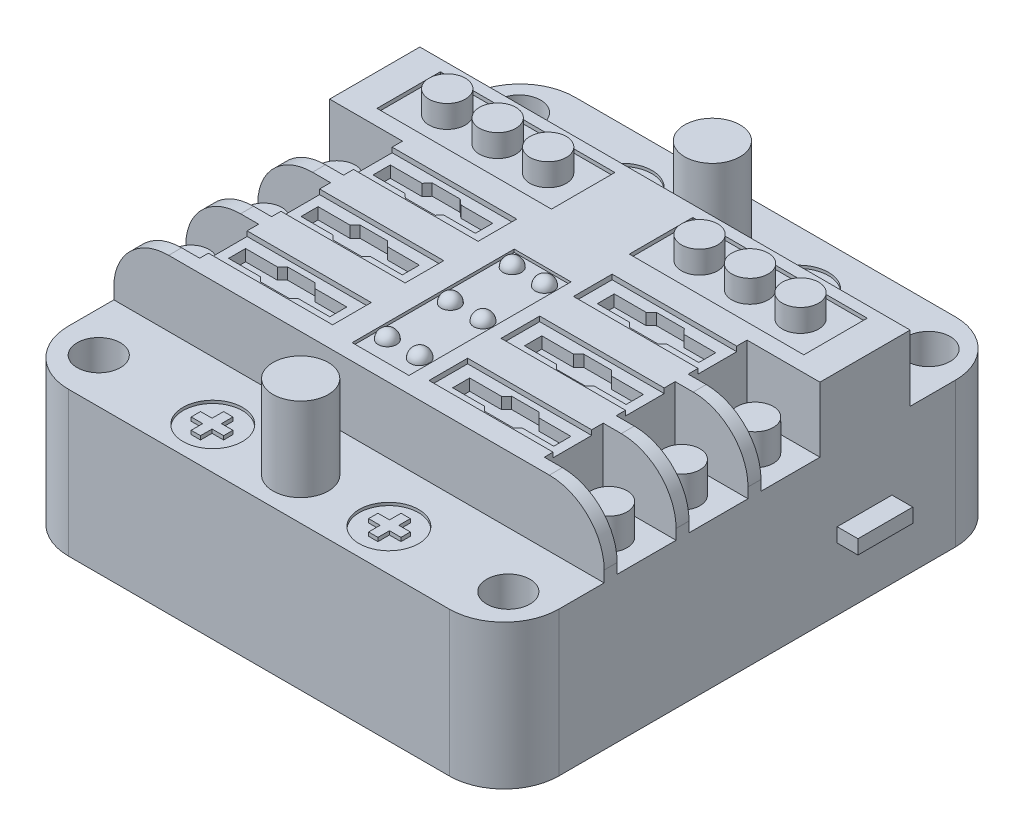
SolidWorks part; units mm, degrees
ref_plane "Front Plane" through (0, 0, 0) normal (0, 0, 1) x (1, 0, 0)
ref_plane "Top Plane" through (0, 0, 0) normal (0, 1, 0) x (1, 0, 0)
ref_plane "Right Plane" through (0, 0, 0) normal (1, 0, 0) x (0, 0, -1)
sketch "Sketch1" plane through (0, 0, 0) normal (0, 1, 0) x (1, 0, 0)
  line L1 (42.5, -43.875) -> (-42.5, -43.875)
  line L2 (42.5, -43.875) -> (42.5, 43.875)
  line L3 (42.5, 43.875) -> (-42.5, 43.875)
  line L4 (-42.5, -43.875) -> (-42.5, 43.875)
  line L5 (42.5, -43.875) -> (-42.5, 43.875) construction
  line L6 (42.5, 43.875) -> (-42.5, -43.875) construction
  point P0 (0, 0)
  dimension "D1" = 87.75
  dimension "D2" = 85
extrude "Boss-Extrude1" add sketch "Sketch1" along normal blind 36.5
sketch "Sketch2" plane through (0, 36.5, 0) normal (0, 1, 0) x (1, 0, 0)
  line L0 (-42.5, 43.875) -> (-42.5, 26.525)
  line L1 (-42.5, 43.875) -> (-42.5, -43.875) construction
  line L2 (-42.5, 26.525) -> (42.5, 26.525)
  line L3 (42.5, -43.875) -> (42.5, 43.875) construction
  line L4 (42.5, 26.525) -> (42.5, 43.875)
  line L5 (42.5, 43.875) -> (-42.5, 43.875)
  dimension "D1" = 17.35
extrude "Cut-Extrude1" cut sketch "Sketch2" against normal blind 11.44
sketch "Sketch3" plane through (0, 36.5, 0) normal (0, 1, 0) x (1, 0, 0)
  line L0 (-42.5, -26.525) -> (-42.5, -43.875)
  line L1 (-42.5, 26.525) -> (-42.5, -43.875) construction
  line L2 (-42.5, -43.875) -> (42.5, -43.875)
  line L3 (42.5, -43.875) -> (42.5, -26.525)
  line L4 (42.5, -43.875) -> (42.5, 26.525) construction
  line L5 (42.5, -26.525) -> (-42.5, -26.525)
  dimension "D1" = 17.35
extrude "Cut-Extrude2" cut sketch "Sketch3" against normal blind 11.44
sketch "Sketch5" plane through (0, 25.06, 0) normal (0, 1, 0) x (1, 0, 0)
  circle A0 centre (0, -36.634) radius 4.8
  dimension "D1" = 9.6
extrude "Boss-Extrude2" add sketch "Sketch5" along normal blind 14.5
sketch "Sketch6" plane through (0, 25.06, 0) normal (0, 1, 0) x (1, 0, 0)
  circle A0 centre (0, 34.7363) radius 4.8
  dimension "D1" = 9.6
extrude "Boss-Extrude3" add sketch "Sketch6" along normal blind 14.5
sketch "Sketch7" plane through (0, 25.06, 0) normal (0, 1, 0) x (1, 0, 0)
  line L0 (-42.5, 43.875) -> (-42.5, 26.525) construction
  line L1 (42.5, 26.525) -> (42.5, 43.875) construction
  circle A0 centre (-35.5, 36.7165) radius 3.75
  circle A1 centre (35.5, 36.7165) radius 3.75
  dimension "D2" = 7.5
  dimension "D3" = 7.5
  dimension "D1" = 7
  dimension "D4" = 7
extrude "Cut-Extrude3" cut sketch "Sketch7" against normal blind 26.5
sketch "Sketch8" plane through (0, 25.06, 0) normal (0, 1, 0) x (1, 0, 0)
  line L0 (-42.5, -26.525) -> (-42.5, -43.875) construction
  line L1 (42.5, -43.875) -> (42.5, -26.525) construction
  circle A0 centre (-35.5, -36.139) radius 3.75
  circle A1 centre (35.5, -36.139) radius 3.75
  point P6 (0, 0)
  dimension "D1" = 7.5
  dimension "D4" = 7.5
  dimension "D2" = 7
  dimension "D3" = 7
extrude "Cut-Extrude4" cut sketch "Sketch8" against normal blind 26.5
sketch "Sketch9" plane through (0, 36.5, 0) normal (0, 1, 0) x (1, 0, 0)
  line L0 (29.87, -14.055) -> (42.5, -14.055)
  line L1 (42.5, -26.525) -> (42.5, 26.525) construction
  line L2 (42.5, -24.275) -> (29.87, -24.275)
  line L3 (29.87, -24.275) -> (29.87, -14.055)
  line L4 (42.5, -14.055) -> (42.5, -24.275)
  line L5 (42.5, -11.805) -> (29.87, -11.805)
  line L6 (29.87, -11.805) -> (29.87, -1.585)
  line L7 (29.87, -1.585) -> (42.5, -1.585)
  line L8 (42.5, 0.665) -> (29.87, 0.665)
  line L9 (29.87, 0.665) -> (29.87, 10.885)
  line L10 (29.87, 10.885) -> (42.5, 10.885)
  line L11 (42.5, 10.885) -> (42.5, 0.665)
  line L12 (42.5, -1.585) -> (42.5, -11.805)
  line L13 (42.5, -26.525) -> (-42.5, -26.525) construction
  dimension "D1" = 10.22
  dimension "D2" = 10.22
  dimension "D3" = 2.25
  dimension "D4" = 10.22
  dimension "D5" = 2.25
  dimension "D6" = 12.63
  dimension "D7" = 2.25
extrude "Cut-Extrude5" cut sketch "Sketch9" against normal blind 11.27
fillet "Fillet1" radius 9.5 3 edges at (42.5, 36.5, 25.4) (42.5, 36.5, 12.93) (42.5, 36.5, 0.46)
sketch "Sketch10" plane through (0, 36.5, 0) normal (0, 1, 0) x (1, 0, 0)
  line L0 (-42.5, -24.275) -> (-29.87, -24.275)
  line L1 (-42.5, 26.525) -> (-42.5, -26.525) construction
  line L2 (-29.87, -24.275) -> (-29.87, -14.055)
  line L3 (-29.87, -14.055) -> (-42.5, -14.055)
  line L4 (-42.5, -14.055) -> (-42.5, -24.275)
  line L5 (-42.5, -11.805) -> (-29.87, -11.805)
  line L6 (-29.87, -11.805) -> (-29.87, -1.585)
  line L7 (-29.87, -1.585) -> (-42.5, -1.585)
  line L8 (-42.5, -1.585) -> (-42.5, -11.805)
  line L9 (-42.5, 0.665) -> (-29.87, 0.665)
  line L10 (-29.87, 0.665) -> (-29.87, 10.885)
  line L11 (-29.87, 10.885) -> (-42.5, 10.885)
  line L12 (-42.5, 10.885) -> (-42.5, 0.665)
  line L13 (42.5, -26.525) -> (-42.5, -26.525) construction
  dimension "D1" = 2.25
  dimension "D2" = 12.63
  dimension "D3" = 10.22
  dimension "D4" = 12.63
  dimension "D5" = 10.22
  dimension "D6" = 12.63
  dimension "D7" = 10.22
  dimension "D8" = 2.25
  dimension "D9" = 2.25
extrude "Cut-Extrude6" cut sketch "Sketch10" against normal blind 11.27
fillet "Fillet2" radius 9.5 3 edges at (-42.5, 36.5, 25.4) (-42.5, 36.5, 12.93) (-42.5, 36.5, 0.46)
sketch "Sketch12" plane through (0, 25.23, 0) normal (0, 1, 0) x (1, 0, 0)
  circle A0 centre (-36.2476, -6.7977) radius 3.15
  circle A1 centre (-36.2476, 5.9101) radius 3.15
  circle A2 centre (-36.2476, -19.4217) radius 3.15
  circle A3 centre (36.2331, -19.4217) radius 3.15
  circle A4 centre (36.2331, -6.7977) radius 3.15
  circle A5 centre (36.2331, 5.9101) radius 3.15
  dimension "D1" = 6.3
  dimension "D2" = 6.3
  dimension "D3" = 6.3
  dimension "D4" = 6.3
  dimension "D5" = 6.3
  dimension "D6" = 6.3
extrude "Boss-Extrude4" add sketch "Sketch12" along normal blind 5.4
sketch "Sketch13" plane through (0, 36.5, 0) normal (0, 1, 0) x (1, 0, 0)
  line L0 (-37, 24.5877) -> (-37, 13.5877)
  line L1 (-37, 13.5877) -> (-6.75, 13.5877)
  line L2 (-6.75, 13.5877) -> (-6.75, 24.5877)
  line L3 (-6.75, 24.5877) -> (-37, 24.5877)
  line L4 (-42.5, 26.525) -> (-42.5, 10.885) construction
  line L5 (37, 24.5877) -> (37, 13.5877)
  line L6 (37, 13.5877) -> (6.75, 13.5877)
  line L7 (6.75, 13.5877) -> (6.75, 24.5877)
  line L8 (6.75, 24.5877) -> (37, 24.5877)
  line L9 (42.5, 10.885) -> (42.5, 26.525) construction
  dimension "D1" = 30.25
  dimension "D2" = 11
  dimension "D3" = 5.5
  dimension "D4" = 5.5
  dimension "D5" = 30.25
  dimension "D6" = 11
extrude "Cut-Extrude7" cut sketch "Sketch13" against normal blind 0.65
sketch "Sketch14" plane through (0, 35.85, 0) normal (0, 1, 0) x (1, 0, 0)
  line L1 (-6.75, 13.5877) -> (-6.75, 24.5877) construction
  circle A0 centre (-30.625, 19.3896) radius 3.15
  circle A1 centre (-21.875, 19.3896) radius 3.15
  circle A2 centre (-13.125, 19.3896) radius 3.15
  circle A3 centre (13.125, 19.3896) radius 3.15
  circle A4 centre (21.875, 19.3896) radius 3.15
  circle A5 centre (30.625, 19.3896) radius 3.15
  point P14 (0, 0)
  point P16 (0, 0)
  point P20 (0, 0)
  point P22 (21.3286, 19.6372)
  point P24 (31.5597, 19.3071)
  dimension "D4" = 6.3
  dimension "D12" = 8.75
  dimension "D10" = 6.375
extrude "Boss-Extrude5" add sketch "Sketch14" along normal blind 3.9
sketch "Sketch15" plane through (0, 25.06, 0) normal (0, 1, 0) x (1, 0, 0)
  circle A0 centre (-15.3, 34.4063) radius 5.15
  circle A1 centre (15.3, 34.4063) radius 5.15
  point P4 (0, 34.7363)
  dimension "D1" = 10.3
  dimension "D2" = 10.3
  dimension "D3" = 15.3
  dimension "D4" = 15.3
extrude "Cut-Extrude8" cut sketch "Sketch15" against normal blind 0.5
sketch "Sketch16" plane through (0, 24.56, 0) normal (0, 1, 0) x (1, 0, 0)
  line L0 (-18.7099, 35.4185) -> (-18.7099, 33.4185)
  line L1 (-18.7099, 33.4185) -> (-12.3799, 33.4185)
  line L2 (-12.3799, 33.4185) -> (-12.3799, 35.4185)
  line L3 (-12.3799, 35.4185) -> (-18.7099, 35.4185)
  line L4 (12.1338, 33.4185) -> (18.4638, 33.4185)
  line L5 (18.4638, 33.4185) -> (18.4638, 35.4185)
  line L6 (18.4638, 35.4185) -> (12.1338, 35.4185)
  line L7 (12.1338, 35.4185) -> (12.1338, 33.4185)
  dimension "D1" = 6.33
  dimension "D2" = 2
  dimension "D3" = 2
  dimension "D4" = 6.33
extrude "Boss-Extrude6" add sketch "Sketch16" along normal blind 0.65
sketch "Sketch18" plane through (0, 25.06, 0) normal (0, 1, 0) x (1, 0, 0)
  circle A0 centre (-15.2229, -36.655) radius 5.15
  circle A1 centre (15.3771, -36.7165) radius 5.15
  point P4 (-10.6761, -36.1114)
  point P7 (0.0771, -36.7165)
  dimension "D3" = 10.3
  dimension "D1" = 15.3
  dimension "D2" = 15.3
extrude "Cut-Extrude9" cut sketch "Sketch18" against normal blind 0.5
sketch "Sketch19" plane through (0, 24.56, 0) normal (0, 1, 0) x (1, 0, 0)
  line L0 (-16.0661, -35.9309) -> (-16.0661, -33.9309)
  line L1 (-16.0661, -33.9309) -> (-14.4461, -33.9309)
  line L2 (-14.4461, -33.9309) -> (-14.4461, -35.9309)
  line L3 (-14.4461, -35.9309) -> (-12.4461, -35.9309)
  line L4 (-12.4461, -35.9309) -> (-12.4461, -37.5509)
  line L5 (-16.0661, -37.5509) -> (-16.0661, -39.5509)
  line L6 (-16.0661, -39.5509) -> (-14.4461, -39.5509)
  line L7 (-14.4461, -39.5509) -> (-14.4461, -37.5509)
  line L8 (-14.4461, -37.5509) -> (-12.4461, -37.5509)
  line L9 (14.5774, -35.8183) -> (14.5774, -33.8183)
  line L10 (14.5774, -33.8183) -> (16.1974, -33.8183)
  line L11 (16.1974, -33.8183) -> (16.1974, -35.8183)
  line L12 (16.1974, -35.8183) -> (18.1974, -35.8183)
  line L13 (18.1974, -35.8183) -> (18.1974, -37.4383)
  line L14 (14.5774, -37.4383) -> (14.5774, -39.4383)
  line L15 (14.5774, -39.4383) -> (16.1974, -39.4383)
  line L16 (16.1974, -39.4383) -> (16.1974, -37.4383)
  line L17 (16.1974, -37.4383) -> (18.1974, -37.4383)
  line L18 (-16.0661, -35.9309) -> (-18.0661, -35.9309)
  line L19 (-18.0661, -35.9309) -> (-18.0661, -37.5509)
  line L20 (-18.0661, -37.5509) -> (-16.0661, -37.5509)
  line L21 (14.5774, -37.4383) -> (12.5774, -37.4383)
  line L22 (12.5774, -37.4383) -> (12.5774, -35.8183)
  line L23 (12.5774, -35.8183) -> (14.5774, -35.8183)
  dimension "D1" = 2
  dimension "D2" = 2
  dimension "D3" = 2
  dimension "D4" = 2
  dimension "D5" = 2
  dimension "D6" = 2
  dimension "D7" = 2
  dimension "D8" = 2
  dimension "D9" = 2
  dimension "D10" = 2
  dimension "D11" = 2
  dimension "D12" = 1.62
  dimension "D13" = 2
  dimension "D14" = 2
  dimension "D15" = 1.62
  dimension "D16" = 1.62
extrude "Boss-Extrude7" add sketch "Sketch19" along normal blind 0.65
sketch "Sketch20" plane through (0, 36.5, 0) normal (0, 1, 0) x (1, 0, 0)
  line L0 (29.87, -1.585) -> (29.87, -11.805) construction
  line L2 (5.87, -12.5085) -> (5.87, 18.9515)
  line L5 (-3.98, 4.365) -> (5.87, 4.365)
  line L6 (-42.5, 26.525) -> (42.5, 26.525) construction
  line L7 (-3.98, 4.365) -> (-3.98, -23.735)
  line L8 (-3.98, -23.735) -> (5.87, -23.735)
  line L9 (5.87, -23.735) -> (5.87, 4.365)
  line L10 (-3.98, 4.365) -> (5.87, 4.365)
  point P0 (0, 0)
  point P8 (29.87, -6.695)
  dimension "D1" = 24
  dimension "D2" = 22.16
  dimension "D3" = 28.1
  dimension "D4" = 9.85
extrude "Cut-Extrude10" cut sketch "Sketch20" against normal blind 0.5 contours L8 L9 L2 L5 L7
sketch "Sketch21" plane through (0, 36, 0) normal (0, 1, 0) x (1, 0, 0)
  line L0 (-3.539, 1.9802) -> (-0.339, 1.9802)
  arc A0 (-0.339, 1.9802) -> (-3.539, 1.9802) centre (-1.939, 1.9802) ccw
  dimension "D1" = 3.2
sketch "Sketch22" plane through (0, 36, 0) normal (0, 1, 0) x (1, 0, 0)
  line L0 (2.0637, 1.9774) -> (5.2637, 1.9774)
  arc A0 (5.2637, 1.9774) -> (2.0637, 1.9774) centre (3.6637, 1.9774) ccw
sketch "Sketch24" plane through (0, 36, 0) normal (0, 1, 0) x (1, 0, 0)
  line L0 (-3.5382, -8.7493) -> (-0.3382, -8.7493)
  arc A0 (-0.3382, -8.7493) -> (-3.5382, -8.7493) centre (-1.9382, -8.7493) ccw
sketch "Sketch25" plane through (0, 36, 0) normal (0, 1, 0) x (1, 0, 0)
  line L0 (2.0755, -8.7061) -> (5.2755, -8.7061)
  arc A0 (5.2755, -8.7061) -> (2.0755, -8.7061) centre (3.6755, -8.7061) ccw
sketch "Sketch26" plane through (0, 36, 0) normal (0, 1, 0) x (1, 0, 0)
  line L0 (-3.5287, -19.6808) -> (-0.3287, -19.6808)
  line L1 (2.0816, -19.6345) -> (5.2816, -19.6345)
  arc A0 (-0.3287, -19.6808) -> (-3.5287, -19.6808) centre (-1.9287, -19.6808) ccw
  arc A1 (5.2816, -19.6345) -> (2.0816, -19.6345) centre (3.6816, -19.6345) ccw
revolve "Revolve2" add sketch "Sketch21" angle 360 about L0
revolve "Revolve3" add sketch "Sketch22" angle 360 about L0
revolve "Revolve4" add sketch "Sketch24" angle 360 about L0
revolve "Revolve5" add sketch "Sketch25" angle 360 about L0
revolve "Revolve6" add sketch "Sketch26" angle 360 about L0
sketch "Sketch27" plane through (0, 36.5, 0) normal (0, 1, 0) x (1, 0, 0)
  line L0 (29.87, 9.0877) -> (8.27, 9.0877)
  line L1 (29.87, 10.885) -> (29.87, 0.665) construction
  line L2 (8.27, 9.0877) -> (8.27, 2.3877)
  line L3 (8.27, 2.3877) -> (29.87, 2.3877)
  line L4 (29.87, 2.3877) -> (29.87, 9.0877)
  line L5 (29.8817, -3.4823) -> (8.2817, -3.4823)
  line L6 (8.2817, -3.4823) -> (8.2817, -10.1823)
  line L7 (8.2817, -10.1823) -> (29.8817, -10.1823)
  line L8 (29.8817, -10.1823) -> (29.8817, -3.4823)
  line L9 (29.9622, -16.0523) -> (8.3622, -16.0523)
  line L10 (8.3622, -16.0523) -> (8.3622, -22.7523)
  line L11 (8.3622, -22.7523) -> (29.9622, -22.7523)
  line L12 (29.9622, -22.7523) -> (29.9622, -16.0523)
  line L13 (-8.3462, -16.0523) -> (-29.9462, -16.0523)
  line L14 (-29.9462, -16.0523) -> (-29.9462, -22.7523)
  line L15 (-29.9462, -22.7523) -> (-8.3462, -22.7523)
  line L16 (-8.3462, -22.7523) -> (-8.3462, -16.0523)
  line L17 (-8.3462, -3.4823) -> (-29.9462, -3.4823)
  line L18 (-29.9462, -3.4823) -> (-29.9462, -10.1823)
  line L19 (-29.9462, -10.1823) -> (-8.3462, -10.1823)
  line L20 (-8.3462, -10.1823) -> (-8.3462, -3.4823)
  line L21 (-8.2708, 9.0877) -> (-29.8708, 9.0877)
  line L22 (-29.8708, 9.0877) -> (-29.8708, 2.3877)
  line L23 (-29.8708, 2.3877) -> (-8.2708, 2.3877)
  line L24 (-8.2708, 2.3877) -> (-8.2708, 9.0877)
  line L25 (6.75, 13.5877) -> (37, 13.5877) construction
  line L26 (-37, 13.5877) -> (-6.75, 13.5877) construction
  dimension "D1" = 6.7
  dimension "D2" = 21.6
  dimension "D3" = 5.87
  dimension "D4" = 5.87
  dimension "D5" = 5.87
  dimension "D6" = 21.6
  dimension "D7" = 4.5
  dimension "D8" = 4.5
  dimension "D9" = 5.87
extrude "Cut-Extrude13" cut sketch "Sketch27" against normal blind 0.85
sketch "Sketch28" plane through (0, 35.65, 0) normal (0, 1, 0) x (1, 0, 0)
  line L0 (-28.2, 7.1022) -> (-28.2, 4.1022)
  line L1 (-28.2, 4.1022) -> (-22.69, 4.1022)
  line L2 (-22.69, 4.1022) -> (-21.9259, 3.4377)
  line L3 (-21.9259, 3.4377) -> (-16.753, 3.4377)
  line L4 (-16.753, 3.4377) -> (-16.0766, 4.2156)
  line L5 (-16.0766, 4.2156) -> (-10.5666, 4.2156)
  line L6 (-10.5666, 4.2156) -> (-10.5666, 7.2156)
  line L8 (-28.2, 7.1022) -> (-22.69, 7.1022)
  line L9 (-22.69, 7.1022) -> (-21.8764, 8.0377)
  line L10 (-21.8764, 8.0377) -> (-17.022, 8.0377)
  line L11 (-17.022, 8.0377) -> (-16.0766, 7.2156)
  line L12 (-16.0766, 7.2156) -> (-10.5666, 7.2156)
  line L13 (-29.87, 9.0877) -> (-29.87, 2.3877) construction
  line L16 (-28.2, -5.4182) -> (-28.2, -8.3682)
  line L17 (-28.2, -8.3682) -> (-22.69, -8.3682)
  line L18 (-22.69, -8.3682) -> (-21.9259, -9.1323)
  line L19 (-21.9259, -9.1323) -> (-16.9001, -9.1323)
  line L20 (-16.9001, -9.1323) -> (-16.1361, -8.3682)
  line L21 (-16.1361, -8.3682) -> (-10.6462, -8.3682)
  line L22 (-10.6462, -8.3682) -> (-10.6462, -5.4182)
  line L23 (-28.2, -5.4182) -> (-22.69, -5.4182)
  line L24 (-22.69, -5.4182) -> (-21.8041, -4.5323)
  line L25 (-21.8041, -4.5323) -> (-17.022, -4.5323)
  line L26 (-17.022, -4.5323) -> (-16.1361, -5.4182)
  line L27 (-16.1361, -5.4182) -> (-10.6462, -5.4182)
  line L28 (-28.2, -17.9882) -> (-28.2, -20.9382)
  line L29 (-28.2, -20.9382) -> (-22.69, -20.9382)
  line L30 (-22.69, -20.9382) -> (-21.9259, -21.7023)
  line L31 (-21.9259, -21.7023) -> (-16.9001, -21.7023)
  line L32 (-16.9001, -21.7023) -> (-16.1361, -20.9382)
  line L33 (-16.1361, -20.9382) -> (-10.6462, -20.9382)
  line L34 (-10.6462, -20.9382) -> (-10.6462, -17.9882)
  line L35 (-28.2, -17.9882) -> (-22.69, -17.9882)
  line L36 (-22.69, -17.9882) -> (-21.8041, -17.1023)
  line L37 (-21.8041, -17.1023) -> (-17.022, -17.1023)
  line L38 (-17.022, -17.1023) -> (-16.1361, -17.9882)
  line L39 (-16.1361, -17.9882) -> (-10.6462, -17.9882)
  line L40 (10.57, 7.1518) -> (10.57, 4.2249)
  line L41 (10.57, 4.2249) -> (16.1598, 4.2249)
  line L42 (16.1598, 4.2249) -> (16.9001, 3.4377)
  line L43 (16.9001, 3.4377) -> (21.9259, 3.4377)
  line L44 (21.9259, 3.4377) -> (22.7131, 4.178)
  line L45 (22.7131, 4.178) -> (28.2, 4.178)
  line L46 (28.2, 4.178) -> (28.2, 7.1251)
  line L47 (10.57, 7.1518) -> (16.08, 7.1518)
  line L48 (16.08, 7.1518) -> (17.022, 8.0377)
  line L49 (17.022, 8.0377) -> (21.8317, 8.0377)
  line L50 (21.8317, 8.0377) -> (22.69, 7.1251)
  line L51 (22.69, 7.1251) -> (28.2, 7.1251)
  line L52 (10.5833, -5.4182) -> (10.5833, -8.4182)
  line L53 (10.5833, -8.4182) -> (16.1361, -8.4182)
  line L54 (16.1361, -8.4182) -> (16.9001, -9.1823)
  line L55 (16.9001, -9.1823) -> (21.9259, -9.1823)
  line L56 (21.9259, -9.1823) -> (22.69, -8.4182)
  line L57 (22.69, -8.4182) -> (28.2, -8.4182)
  line L58 (28.2, -8.4182) -> (28.2, -5.4182)
  line L59 (10.5833, -5.4182) -> (16.0933, -5.4182)
  line L60 (16.0933, -5.4182) -> (16.9793, -4.5323)
  line L61 (16.9793, -4.5323) -> (21.8041, -4.5323)
  line L62 (21.8041, -4.5323) -> (22.69, -5.4182)
  line L63 (22.69, -5.4182) -> (28.2, -5.4182)
  line L64 (10.6622, -18.0002) -> (10.6622, -20.9487)
  line L65 (10.6622, -20.9487) -> (16.1619, -20.9487)
  line L66 (16.1619, -20.9487) -> (16.9363, -21.7023)
  line L67 (16.9363, -21.7023) -> (21.9621, -21.7023)
  line L68 (21.9621, -21.7023) -> (22.69, -20.9543)
  line L69 (22.69, -20.9543) -> (28.2, -20.9543)
  line L70 (28.2, -20.9543) -> (28.2, -17.9882)
  line L71 (10.6622, -18.0002) -> (16.1722, -18.0002)
  line L72 (16.1722, -18.0002) -> (17.046, -17.1023)
  line L73 (17.046, -17.1023) -> (21.7796, -17.1023)
  line L74 (21.7796, -17.1023) -> (22.69, -17.9882)
  line L75 (22.69, -17.9882) -> (28.2, -17.9882)
  line L76 (-29.87, -3.4823) -> (-29.87, -10.1823) construction
  line L77 (-29.87, 2.3877) -> (-8.2708, 2.3877) construction
  line L78 (-8.2708, 9.0877) -> (-29.87, 9.0877) construction
  line L79 (-29.87, -10.1823) -> (-8.3462, -10.1823) construction
  line L80 (-8.3462, -3.4823) -> (-29.87, -3.4823) construction
  line L81 (-29.87, -24.275) -> (-29.87, -14.055) construction
  line L82 (-8.3462, -16.0523) -> (-29.87, -16.0523) construction
  line L83 (-29.87, -22.7523) -> (-8.3462, -22.7523) construction
  line L84 (29.87, 2.3877) -> (29.87, 9.0877) construction
  line L85 (29.87, 9.0877) -> (8.27, 9.0877) construction
  line L86 (8.27, 2.3877) -> (29.87, 2.3877) construction
  line L87 (29.87, -3.4823) -> (8.2817, -3.4823) construction
  line L88 (29.87, -1.585) -> (29.87, -11.805) construction
  line L89 (8.2817, -3.4823) -> (8.2817, -10.1823) construction
  line L90 (8.27, 9.0877) -> (8.27, 2.3877) construction
  line L91 (-8.2708, 2.3877) -> (-8.2708, 9.0877) construction
  line L92 (-8.3462, -10.1823) -> (-8.3462, -3.4823) construction
  line L93 (-8.3462, -22.7523) -> (-8.3462, -16.0523) construction
  line L94 (8.3622, -16.0523) -> (8.3622, -22.7523) construction
  line L95 (29.87, -14.055) -> (29.87, -24.275) construction
  line L96 (29.87, -16.0523) -> (8.3622, -16.0523) construction
  line L97 (8.3622, -22.7523) -> (29.87, -22.7523) construction
  dimension "D1" = 3
  dimension "D2" = 5.51
  dimension "D3" = 3
  dimension "D4" = 1.67
  dimension "D5" = 5.51
  dimension "D6" = 5.51
  dimension "D7" = 5.51
  dimension "D8" = 1.67
  dimension "D9" = 1.05
  dimension "D10" = 1.05
  dimension "D11" = 1.05
  dimension "D12" = 1.05
  dimension "D13" = 1.67
  dimension "D14" = 1.05
  dimension "D15" = 1.05
  dimension "D16" = 1.67
  dimension "D17" = 1.05
  dimension "D18" = 1.05
  dimension "D19" = 1.05
  dimension "D20" = 1.67
  dimension "D21" = 2.3016
  dimension "D22" = 2.3
  dimension "D23" = 2.2958
  dimension "D24" = 2.3
  dimension "D25" = 2.3
  dimension "D26" = 2.3
  dimension "D27" = 1.67
  dimension "D28" = 1.05
  dimension "D29" = 1.05
  dimension "D30" = 5.51
  dimension "D31" = 5.51
  dimension "D32" = 5.51
  dimension "D33" = 5.51
  dimension "D34" = 5.51
  dimension "D35" = 5.51
  dimension "D36" = 5.51
  dimension "D37" = 5.51
extrude "Cut-Extrude14" cut sketch "Sketch28" against normal blind 2
fillet "Fillet3" radius 9.5 4 edges at (42.5, 12.53, -43.875) (42.5, 12.53, 43.875) (-42.5, 12.53, 43.875) (-42.5, 12.53, -43.875)
sketch "Sketch29" plane through (-42.5, 0, 0) normal (-1, 0, 0) x (0, 0, 1)
  line L0 (-23.375, 10.85) -> (-13.875, 10.85)
  line L1 (-13.875, 10.85) -> (-13.875, 13.3)
  line L2 (-13.875, 13.3) -> (-23.375, 13.3)
  line L3 (-23.375, 13.3) -> (-23.375, 10.85)
  line L4 (-34.375, 0) -> (34.375, 0) construction
  line L5 (-34.375, 25.06) -> (-34.375, 0) construction
  dimension "D1" = 10.85
  dimension "D2" = 2.45
  dimension "D3" = 9.5
  dimension "D4" = 11
extrude "Boss-Extrude9" add sketch "Sketch29" along normal blind 3.6
sketch "Sketch30" plane through (42.5, 0, 0) normal (1, 0, 0) x (0, 0, -1)
  line L0 (13.875, 10.85) -> (23.375, 10.85)
  line L1 (23.375, 10.85) -> (23.375, 13.3)
  line L2 (23.375, 13.3) -> (13.875, 13.3)
  line L3 (13.875, 13.3) -> (13.875, 10.85)
  line L4 (34.375, 0) -> (34.375, 25.06) construction
  line L5 (-34.375, 0) -> (34.375, 0) construction
  dimension "D1" = 11
  dimension "D2" = 10.85
extrude "Boss-Extrude10" add sketch "Sketch30" along normal blind 3.6
